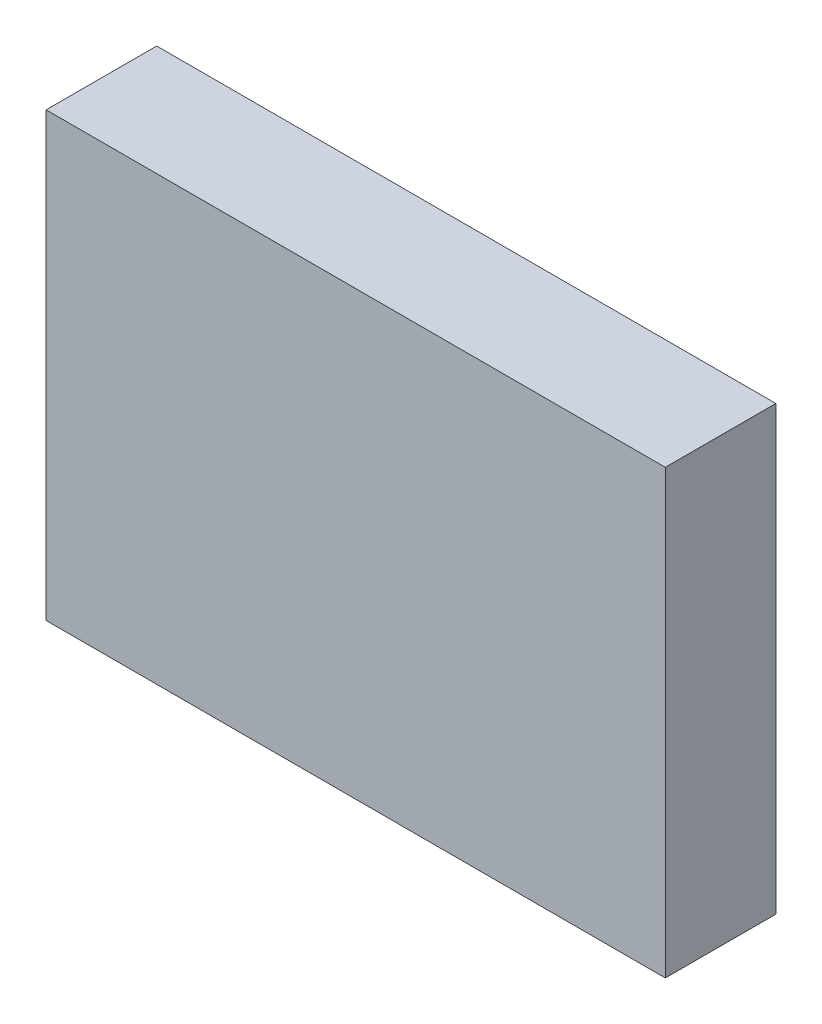
SolidWorks part; units mm, degrees
ref_plane "Front Plane" through (0, 0, 0) normal (0, 0, 1) x (1, 0, 0)
ref_plane "Top Plane" through (0, 0, 0) normal (0, 1, 0) x (1, 0, 0)
ref_plane "Right Plane" through (0, 0, 0) normal (1, 0, 0) x (0, 0, -1)
sketch "Sketch1" plane through (0, 0, 0) normal (0, 0, 1) x (1, 0, 0)
  line L1 (-14, 10) -> (14, 10)
  line L2 (-14, 10) -> (-14, -10)
  line L3 (-14, -10) -> (14, -10)
  line L4 (14, 10) -> (14, -10)
  line L5 (-14, 10) -> (14, -10) construction
  line L6 (-14, -10) -> (14, 10) construction
  point P0 (0, 0)
  dimension "D1" = 28
  dimension "D2" = 20
extrude "Boss-Extrude1" add sketch "Sketch1" along normal blind 5
